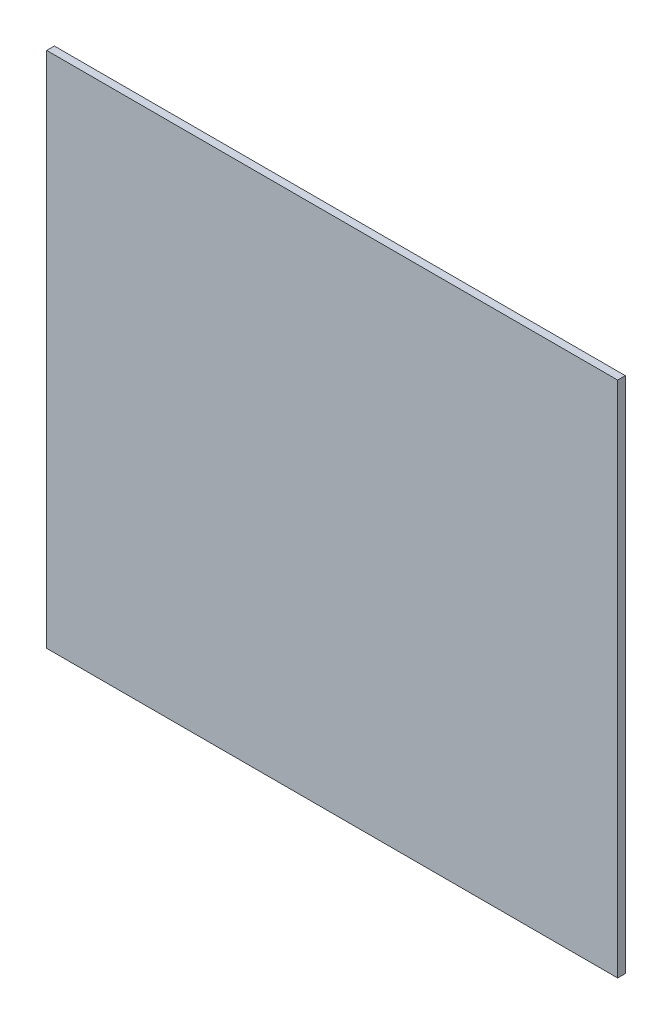
SolidWorks part; units mm, degrees
ref_plane "Front Plane" through (0, 0, 0) normal (0, 0, 1) x (1, 0, 0)
ref_plane "Top Plane" through (0, 0, 0) normal (0, 1, 0) x (1, 0, 0)
ref_plane "Right Plane" through (0, 0, 0) normal (1, 0, 0) x (0, 0, -1)
sketch "Sketch1" plane through (0, 0, 0) normal (0, 0, 1) x (1, 0, 0)
  line L1 (-161.925, -146.8628) -> (161.925, -146.8628)
  line L2 (-161.925, -146.8628) -> (-161.925, 146.8628)
  line L3 (-161.925, 146.8628) -> (161.925, 146.8628)
  line L4 (161.925, -146.8628) -> (161.925, 146.8628)
  line L5 (-161.925, -146.8628) -> (161.925, 146.8628) construction
  line L6 (-161.925, 146.8628) -> (161.925, -146.8628) construction
  point P0 (0, 0)
  dimension "D1" = 293.7256
  dimension "D2" = 323.85
extrude "Boss-Extrude1" add sketch "Sketch1" along normal blind 4.3434
